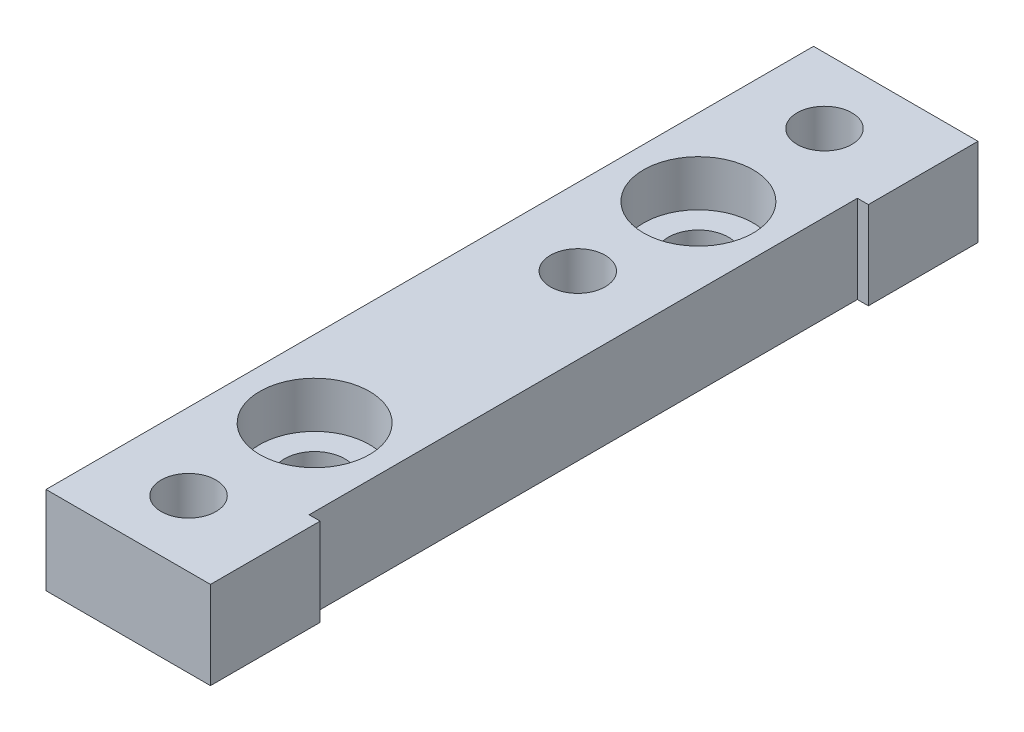
SolidWorks part; units mm, degrees
ref_plane "Front Plane" through (0, 0, 0) normal (0, 0, 1) x (1, 0, 0)
ref_plane "Top Plane" through (0, 0, 0) normal (0, 1, 0) x (1, 0, 0)
ref_plane "Right Plane" through (0, 0, 0) normal (1, 0, 0) x (0, 0, -1)
sketch "Sketch1" plane through (0, 0, 0) normal (0, 1, 0) x (1, 0, 0)
  line L1 (-7.5, 35) -> (7.5, 35)
  line L2 (-7.5, 35) -> (-7.5, -35)
  line L3 (-7.5, -35) -> (7.5, -35)
  line L4 (7.5, 35) -> (7.5, -35)
  line L5 (-7.5, 35) -> (7.5, -35) construction
  line L6 (-7.5, -35) -> (7.5, 35) construction
  point P0 (0, 0)
  dimension "D1" = 15
  dimension "D2" = 70
extrude "Boss-Extrude1" add sketch "Sketch1" along normal blind 8
sketch "Sketch2" plane through (0, 8, 0) normal (0, 1, 0) x (1, 0, 0)
  line L0 (7.5, -35) -> (7.5, 35) construction
  line L1 (7.5, 25) -> (6.5, 25)
  line L2 (7.5, 25) -> (7.5, -25)
  line L3 (7.5, -25) -> (6.5, -25)
  line L4 (6.5, 25) -> (6.5, -25)
  line L5 (-7.5, -35) -> (7.5, -35) construction
  line L6 (7.5, 35) -> (-7.5, 35) construction
  dimension "D1" = 1
  dimension "D2" = 10
  dimension "D3" = 10
extrude "Cut-Extrude1" cut sketch "Sketch2" against normal blind 8
sketch "Sketch3" plane through (0, 8, 0) normal (0, 1, 0) x (1, 0, 0)
  line L0 (-7.5, 35) -> (-7.5, -35) construction
  line L1 (7.5, 35) -> (-7.5, 35) construction
  line L2 (-7.5, -35) -> (7.5, -35) construction
  circle A0 centre (-0.5, -29) radius 2.5
  circle A1 centre (-0.5, 29) radius 2.5
  dimension "D1" = 7
  dimension "D2" = 6
  dimension "D3" = 6
  dimension "D4" = 7
extrude "Cut-Extrude2" cut sketch "Sketch3" against normal blind 8
sketch "Sketch4" plane through (0, 8, 0) normal (0, 1, 0) x (1, 0, 0)
  line L0 (-7.5, 35) -> (-7.5, -35) construction
  line L1 (-7.5, -35) -> (7.5, -35) construction
  line L2 (7.5, 35) -> (-7.5, 35) construction
  circle A0 centre (-0.5, -17.5) radius 2.75
  circle A1 centre (-0.5, 17.5) radius 2.75
  point P6 (0, 0)
  dimension "D1" = 7
  dimension "D2" = 7
  dimension "D3" = 17.5
  dimension "D4" = 17.5
extrude "Cut-Extrude3" cut sketch "Sketch4" against normal blind 8
sketch "Sketch5" plane through (0, 8, 0) normal (0, 1, 0) x (1, 0, 0)
  circle A0 centre (-0.5, 17.5) radius 5
  circle A1 centre (-0.5, -17.5) radius 5
extrude "Cut-Extrude4" cut sketch "Sketch5" against normal blind 4.2
sketch "Sketch6" plane through (0, 8, 0) normal (0, 1, 0) x (1, 0, 0)
  line L0 (-7.5, 35) -> (-7.5, -35) construction
  line L1 (-7.5, -35) -> (7.5, -35) construction
  circle A0 centre (-0.5, 6.5) radius 2.5
  dimension "D1" = 7
  dimension "D2" = 41.5
extrude "Cut-Extrude5" cut sketch "Sketch6" against normal blind 72.2
